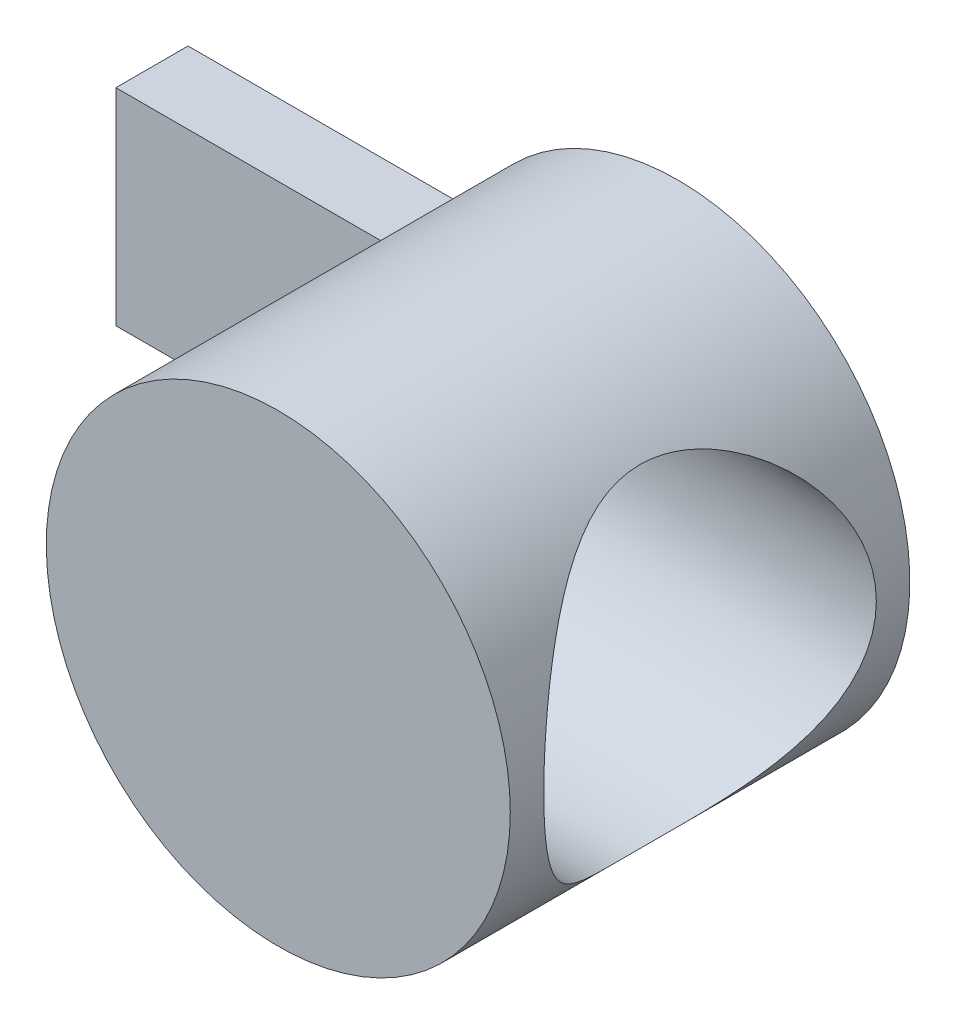
SolidWorks part; units mm, degrees
material "ЦА4М3 ГОСТ 25140-93"
ref_plane "Спереди" through (0, 0, 0) normal (0, 0, 1) x (1, 0, 0)
ref_plane "Сверху" through (0, 0, 0) normal (0, 1, 0) x (1, 0, 0)
ref_plane "Справа" through (0, 0, 0) normal (1, 0, 0) x (0, 0, -1)
sketch "Эскиз1" plane through (0, 0, 0) normal (0, 0, 1) x (1, 0, 0)
  circle A0 centre (0, 0) radius 9
  dimension "D1" = 9
extrude "Бобышка-Вытянуть1" add sketch "Эскиз1" along normal blind 15.5
sketch "Эскиз2" plane through (0, 0, 0) normal (0, 0, 1) x (1, 0, 0)
  line L1 (-8.0623, 4) -> (-19, 4)
  line L2 (-8.0623, 4) -> (-8.0623, -4)
  line L3 (-8.0623, -4) -> (-19, -4)
  line L4 (-19, 4) -> (-19, -4)
  circle A0 centre (0, 0) radius 9 construction
  dimension "D1" = 28
  dimension "D2" = 8
extrude "Бобышка-Вытянуть2" add sketch "Эскиз2" along normal blind 2.8
sketch "Эскиз3" plane through (0, 0, 0) normal (1, 0, 0) x (0, 0, -1)
  line L0 (-7.75, 9) -> (-7.75, 0) construction
  line L1 (0, 9) -> (-15.5, 9) construction
  circle A0 centre (-7.75, 0) radius 6.45
  dimension "D1" = 12.9
extrude "Вырез-Вытянуть1" cut sketch "Эскиз3" along normal through all and the other way blind 2
sketch "Эскиз4" plane through (-2, 0, 0) normal (1, 0, 0) x (0, 0, -1)
  circle A0 centre (-7.75, 0) radius 4
  dimension "D1" = 8
extrude "Вырез-Вытянуть2" cut sketch "Эскиз4" against normal through all
